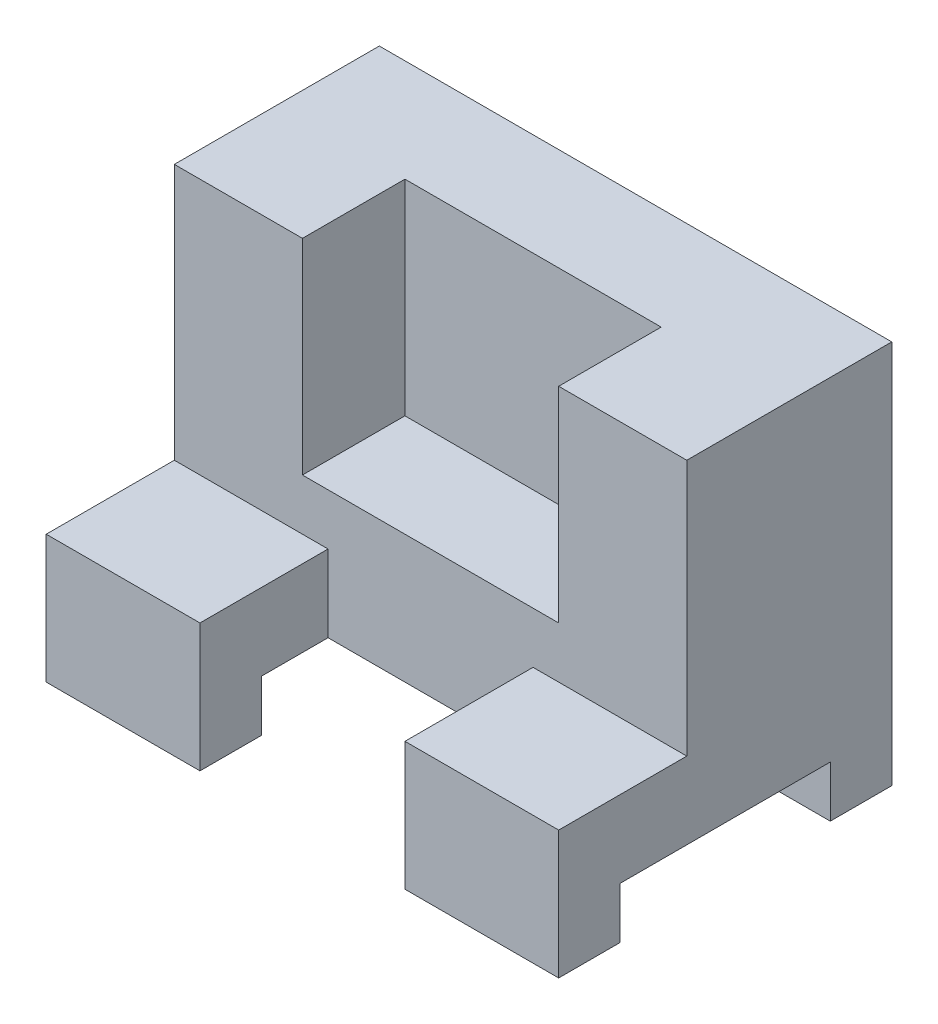
SolidWorks part; units mm, degrees
ref_plane "Front Plane" through (0, 0, 0) normal (0, 0, 1) x (1, 0, 0)
ref_plane "Top Plane" through (0, 0, 0) normal (0, 1, 0) x (1, 0, 0)
ref_plane "Right Plane" through (0, 0, 0) normal (1, 0, 0) x (0, 0, -1)
sketch "Sketch1" plane through (0, 0, 0) normal (0, 1, 0) x (1, 0, 0)
  line L1 (-56.1562, -22.5075) -> (43.8438, -22.5075)
  line L2 (-56.1562, -22.5075) -> (-56.1562, 42.4925)
  line L3 (-56.1562, 42.4925) -> (43.8438, 42.4925)
  line L4 (43.8438, -22.5075) -> (43.8438, 42.4925)
extrude "Boss-Extrude1" add sketch "Sketch1" along normal blind 75
sketch3d "3DSketch1" plane through (0, 0, 0) normal (0, 0, 1) x (1, 0, 0)
  dimension "D1" = 10
sketch3d "3DSketch2" plane through (0, 0, 0) normal (0, 0, 1) x (1, 0, 0)
sketch "Sketch5" plane through (43.8438, 0, 0) normal (1, 0, 0) x (0, 0, -1)
  line L3 (-22.5075, 0) -> (42.4925, 0) construction
  line L4 (-10.5075, 0) -> (-10.5075, 10)
  line L6 (30.4925, 0) -> (30.4925, 10)
  line L7 (30.4925, 10) -> (-10.5075, 10)
  line L8 (-10.5075, 0) -> (30.4925, 0)
extrude "Cut-Extrude1" cut sketch "Sketch5" against normal blind 141
sketch "Sketch6" plane through (0, 75, 0) normal (0, 1, 0) x (1, 0, 0)
  line L0 (43.8438, -22.5075) -> (43.8438, 42.4925) construction
  line L1 (-56.1562, 42.4925) -> (43.8438, 42.4925)
  line L2 (-56.1562, 42.4925) -> (-56.1562, 2.4925)
  line L3 (-56.1562, 2.4925) -> (43.8438, 2.4925)
  line L4 (43.8438, 42.4925) -> (43.8438, 2.4925)
  line L6 (-56.1562, 2.4925) -> (43.8438, 2.4925)
  line L7 (-56.1562, 2.4925) -> (-56.1562, -22.5075)
  line L8 (-56.1562, -22.5075) -> (43.8438, -22.5075)
  line L9 (43.8438, 2.4925) -> (43.8438, -22.5075)
  line M1 (-56.1562, 42.4925) -> (-56.1562, -22.5075)
  line M3 (43.8438, -22.5075) -> (43.8438, 42.4925)
  line M4 (43.8438, 42.4925) -> (-56.1562, 42.4925)
extrude "Cut-Extrude2" cut sketch "Sketch6" against normal blind 50 and the other way through all flip side to cut contours L3 M1 M3 M4
sketch "Sketch7" plane through (0, 75, 0) normal (0, 1, 0) x (1, 0, 0)
  line L0 (-31.1562, 2.4925) -> (18.8438, 2.4925)
  line L1 (-56.1562, 2.4925) -> (43.8438, 2.4925) construction
  line L2 (-31.1562, 2.4925) -> (-31.1562, 22.4925)
  line L3 (-31.1562, 22.4925) -> (18.8438, 22.4925)
  line L4 (18.8438, 22.4925) -> (18.8438, 2.4925)
  line L5 (-56.1562, 2.4925) -> (43.8438, 2.4925) construction
  line L6 (18.8438, 2.4925) -> (-31.1562, 2.4925)
  line M3 (-56.1562, 2.4925) -> (43.8438, 2.4925)
extrude "Cut-Extrude3" cut sketch "Sketch7" against normal blind 40 contours L4 L3 L2 M3
sketch "Sketch10" plane through (0, 25, 0) normal (0, 1, 0) x (1, 0, 0)
  line L0 (-56.1562, 2.4925) -> (43.8438, 2.4925) construction
  line L4 (13.8438, -22.5075) -> (13.8438, 2.4925)
  line L9 (-26.1562, -22.5075) -> (-26.1562, 2.4925)
  line L10 (-26.1562, -22.5075) -> (13.8438, -22.5075)
  line L11 (-26.1562, -22.5075) -> (-26.1562, 2.4925)
  line L12 (-26.1562, 2.4925) -> (13.8438, 2.4925)
  line L13 (13.8438, -22.5075) -> (13.8438, 2.4925)
  line M4 (-56.1562, -22.5075) -> (43.8438, -22.5075)
  line M6 (43.8438, 2.4925) -> (-56.1562, 2.4925)
extrude "Cut-Extrude4" cut sketch "Sketch10" against normal blind 40 contours L9 L4 M4 M6
